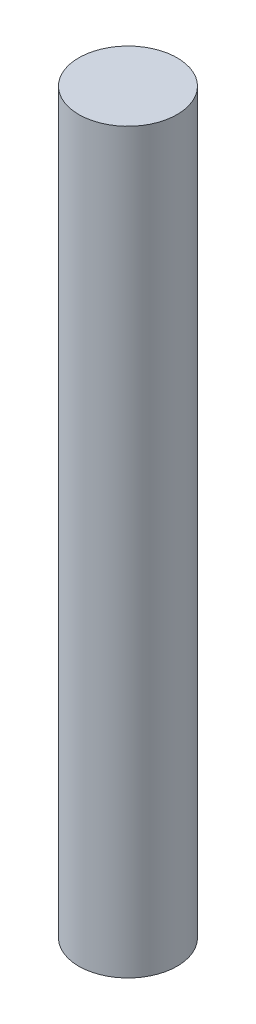
SolidWorks part; units mm, degrees
ref_plane "Front Plane" through (0, 0, 0) normal (0, 0, 1) x (1, 0, 0)
ref_plane "Top Plane" through (0, 0, 0) normal (0, 1, 0) x (1, 0, 0)
ref_plane "Right Plane" through (0, 0, 0) normal (1, 0, 0) x (0, 0, -1)
sketch "Sketch1" plane through (0, 0, 0) normal (0, 1, 0) x (1, 0, 0)
  circle A0 centre (-8.9844, 7.0711) radius 4
  dimension "D1" = 8
extrude "Boss-Extrude1" add sketch "Sketch1" along normal blind 60
